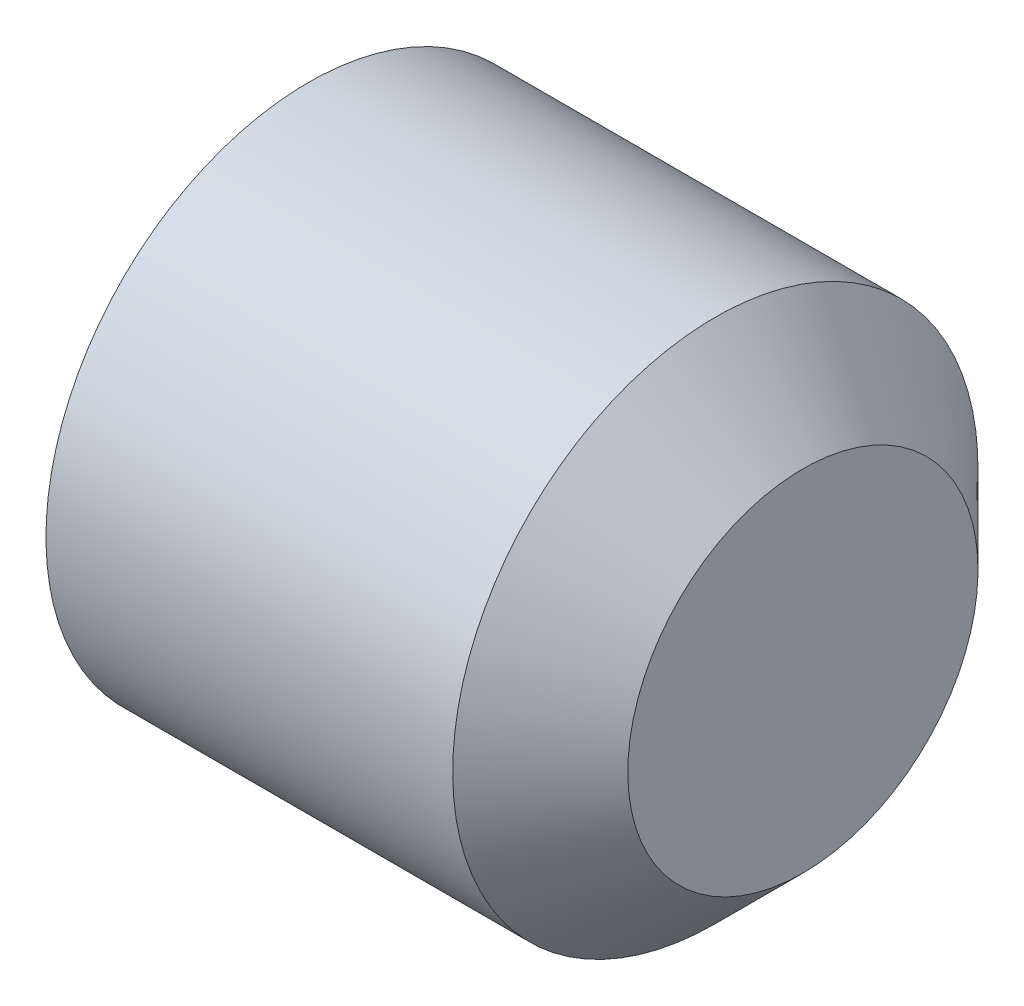
SolidWorks part; units mm, degrees
ref_plane "Front Plane" through (0, 0, 0) normal (0, 0, 1) x (1, 0, 0)
ref_plane "Top Plane" through (0, 0, 0) normal (0, 1, 0) x (1, 0, 0)
ref_plane "Right Plane" through (0, 0, 0) normal (1, 0, 0) x (0, 0, -1)
ref_plane "Plane1" through (0, 0, 0) normal (0, 0, 1) x (1, 0, 0)
sketch "Sketch1" plane through (0, 0, 0) normal (0, 0, 1) x (1, 0, 0)
  line L0 (6, 0) -> (6, -2)
  line L1 (6, -2) -> (5, -3)
  line L2 (5, -3) -> (0.3542, -3)
  line L3 (0.3542, -3) -> (0, -2.3865)
  line L4 (0, -2.3865) -> (0, -1.7321)
  line L5 (0, -1.7321) -> (1, 0)
  line L6 (1, 0) -> (6, 0)
  line L7 (1, 0) -> (6, 0) construction
revolve "Revolve1" add sketch "Sketch1" angle 360 about L7
ref_plane "Plane2" through (0, 0, 0) normal (1, 0, 0) x (0, 0, -1)
sketch "Sketch2" plane through (0, 0, 0) normal (1, 0, 0) x (0, 0, -1)
  line L0 (-1.7321, 0) -> (-0.866, -1.5)
  line L1 (-0.866, -1.5) -> (0.866, -1.5)
  line L2 (0.866, -1.5) -> (1.7321, 0)
  line L3 (1.7321, 0) -> (0.866, 1.5)
  line L4 (0.866, 1.5) -> (-0.866, 1.5)
  line L5 (-0.866, 1.5) -> (-1.7321, 0)
extrude "Cut-Extrude1" cut sketch "Sketch2" along normal blind 2
